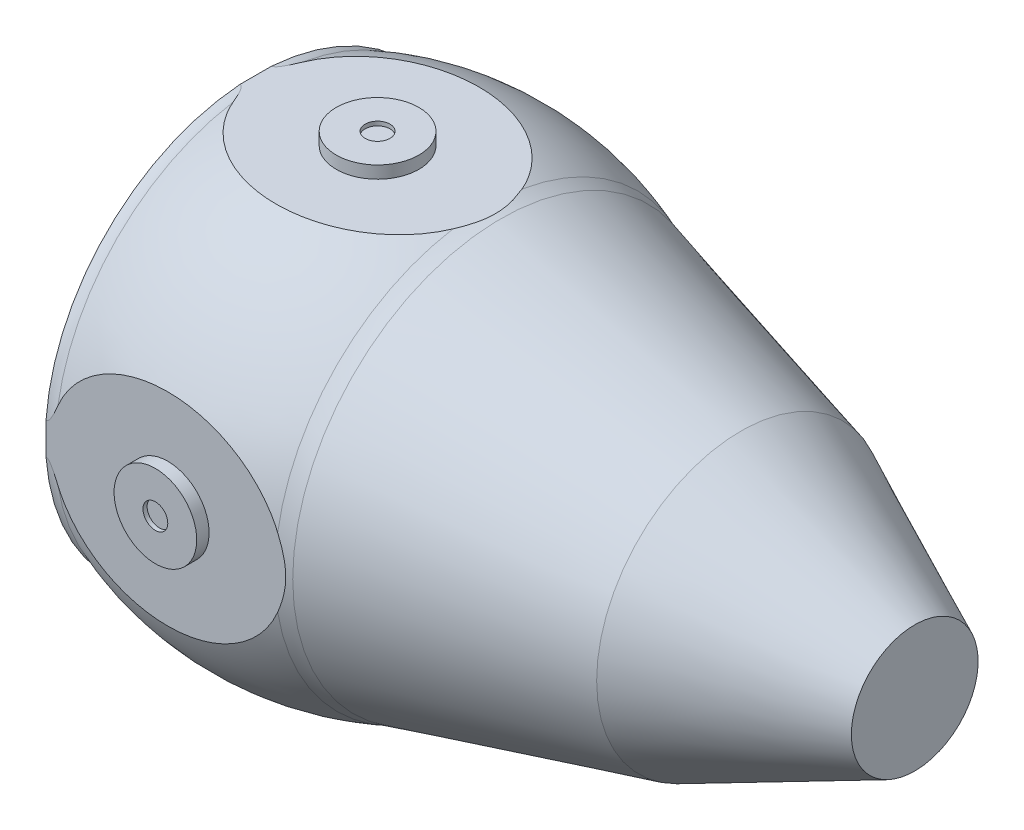
SolidWorks part; units mm, degrees
material "ABS"
ref_plane "Plano frontal" through (0, 0, 0) normal (0, 0, 1) x (1, 0, 0)
ref_plane "Plano superior" through (0, 0, 0) normal (0, 1, 0) x (1, 0, 0)
ref_plane "Plano direito" through (0, 0, 0) normal (1, 0, 0) x (0, 0, -1)
sketch "Esboço1" plane through (0, 0, 0) normal (0, 0, 1) x (1, 0, 0)
  line L0 (0, 0) -> (0, 2210.2124) construction
  line L1 (0, 0) -> (169.4374, 0) construction
  line L2 (3250.5369, 0) -> (3250.5369, 383.5)
  line L3 (3250.5369, 383.5) -> (2198.5369, 873)
  line L4 (2198.5369, 873) -> (746.5369, 1260)
  line L5 (0, -439.8614) -> (665, 1286.4859) construction
  line L6 (0, -439.8614) -> (-665, 1286.4859) construction
  line L7 (-736.8919, 1273.118) -> (-1420, 1273.118) construction
  line L8 (-3866.8673, 2245.4829) -> (-3866.8673, 0) construction
  line L9 (-169.4374, 0) -> (169.4374, 0) construction
  line L10 (-1420, 1273.118) -> (-3610, 2160) construction
  line L11 (-3866.8673, 2245.4829) -> (-3861.047, 2245.4829) construction
  line L12 (-3866.8673, 2378.8809) -> (-3991.8673, 2378.8809) construction
  line L13 (-1422.922, 1258.118) -> (-3618.297, 2147.1767) construction
  line L14 (-6965, 15) -> (3235.5369, 15) construction
  line L15 (2193.4021, 858.8449) -> (742.6738, 1245.506) construction
  line L16 (-6630, 350) -> (2492.8949, 350) construction
  line L17 (-736.8919, 1258.118) -> (-1422.922, 1258.118) construction
  line L18 (-4829, 2860) -> (-6980, 3864) construction
  line L19 (-4834.2705, 2845.9065) -> (-6965, 3840.4451) construction
  line L20 (-6980, 0) -> (3250.5369, 0) construction
  line L21 (-3991.8673, 0) -> (-3866.8673, 0) construction
  line L22 (3235.5369, 0) -> (-3866.8673, 0) construction
  line L23 (3235.5369, 373.9352) -> (2193.4021, 858.8449)
  line L24 (2193.4021, 858.8449) -> (1303.3383, 1096.0727)
  line L25 (-1317.1289, 1258.118) -> (-1422.922, 1258.118) construction
  line L26 (-1422.922, 1258.118) -> (-3861.047, 2245.4829) construction
  line L27 (-3991.8673, 2378.8809) -> (-3991.8673, 0) construction
  line L28 (-1317.1289, 1258.118) -> (-736.8919, 923.118) construction
  line L29 (656.3984, 921.8062) -> (746.5369, 946.0868) construction
  line L30 (3250.5369, 0) -> (3235.5369, 0)
  line L31 (-736.8919, 923.118) -> (-1488.1803, 923.118) construction
  line L32 (-1488.1803, 923.118) -> (-3805.5661, 1861.5873) construction
  line L33 (-4951.2113, 2530.7942) -> (-6630, 3314.385) construction
  line L34 (-6630, 3314.385) -> (-6630, 350) construction
  line L35 (2078.7249, 542.715) -> (656.3984, 921.8062) construction
  line L36 (2492.8949, 350) -> (2078.7249, 542.715) construction
  line L37 (2492.8949, 350) -> (2492.8949, 350) construction
  line L38 (-6965, 3840.4451) -> (-6965, 15) construction
  line L39 (-6980, 3864) -> (-6980, 0) construction
  line L40 (3235.5369, 0) -> (3235.5369, 373.9352)
  line L41 (746.5369, 1260) -> (746.5369, 1244.4764) construction
  line L42 (3235.5369, 15) -> (3235.5369, 373.9352) construction
  line L43 (746.5369, 946.0868) -> (1303.3383, 1096.0727) construction
  line L44 (1303.3383, 1096.0727) -> (746.5369, 1244.4764)
  line L45 (746.5369, 1244.4764) -> (746.5369, 946.0868) construction
  line L46 (746.5369, 1244.4764) -> (71.7181, 1244.4764)
  line L47 (-736.8919, 1273.118) -> (-736.8919, 1244.4764)
  line L48 (41.7181, 1244.4764) -> (41.7181, 1164.4764)
  line L49 (41.7181, 1164.4764) -> (71.7181, 1164.4764)
  line L50 (71.7181, 1164.4764) -> (71.7181, 1244.4764)
  line L51 (41.7181, 1244.4764) -> (-736.8919, 1244.4764)
  arc A0 (665, 1286.4859) -> (-665, 1286.4859) centre (0, -439.8614) ccw
  arc A1 (746.5369, 1260) -> (665, 1286.4859) centre (952.5676, 2033.0145) cw
  arc A2 (-736.8919, 1273.118) -> (-665, 1286.4859) centre (-736.8919, 1473.118) ccw
  arc A3 (-3610, 2160) -> (-3866.8673, 2378.8809) centre (-5637.2528, 41.0847) ccw construction
  arc A4 (656.3984, 921.8062) -> (539.1892, 959.8796) centre (952.5676, 2033.0145) cw construction
  arc A5 (539.1892, 959.8796) -> (-539.1892, 959.8796) centre (0, -439.8614) ccw construction
  arc A6 (-736.8919, 923.118) -> (-539.1892, 959.8796) centre (-736.8919, 1473.118) ccw construction
  arc A8 (659.6081, 1272.4885) -> (-659.6081, 1272.4885) centre (0, -439.8614) ccw construction
  arc A9 (-3618.297, 2147.1767) -> (-4834.2705, 2845.9065) centre (-5637.2528, 41.0847) ccw construction
  arc A10 (-3610, 2160) -> (-4829, 2860) centre (-5637.2528, 41.0847) ccw construction
  arc A12 (-3805.5661, 1861.5873) -> (-4951.2113, 2530.7942) centre (-5637.2528, 41.0847) ccw construction
  arc A13 (742.6738, 1245.506) -> (659.6081, 1272.4885) centre (952.5676, 2033.0145) cw construction
  arc A14 (-736.8919, 1258.118) -> (-659.6081, 1272.4885) centre (-736.8919, 1473.118) ccw construction
  point P17 (-4829, 2860)
  point P56 (-8569.7525, 41.0847)
  dimension "D1" = 800
  dimension "D7" = 1850
  dimension "D9" = 200
  dimension "D11" = 3610
  dimension "D14" = 2160
  dimension "D15" = 5865
  dimension "D2" = 767
  dimension "D3" = 1746
  dimension "D4" = 1052
  dimension "D5" = 2520
  dimension "D6" = 1452
  dimension "D8" = 1330
  dimension "D10" = 1420
  dimension "D12" = 4829
  dimension "D13" = 2860
  dimension "D16" = 5.8203
  dimension "D17" = 125
  dimension "D20" = 150
  dimension "D21" = 150
  dimension "D22" = 7242.4042
  dimension "D23" = 125
  dimension "D24" = 808.61
  dimension "D25" = 30
  dimension "D26" = 80
  dimension "D18" = 350
  dimension "D19" = 15
revolve "Revolução1" add sketch "Esboço1" angle 360 about L9
scale "Escala1" scale about origin uniform scaling yes scale factor 0.2
sketch "Esboço2" plane through (0, 0, 0) normal (0, 0, 1) x (1, 0, 0)
  line L0 (149.3074, 248.8953) -> (14.3436, 248.8953) construction
  line L2 (15, 268.8953) -> (15, 263.8953)
  line L3 (15, 263.8953) -> (0, 263.8953)
  line L4 (15, 268.8953) -> (50, 268.8953)
  line L5 (50, 268.8953) -> (50, 253.8953)
  line L6 (50, 253.8953) -> (175.533, 253.8953)
  line L8 (175.533, 253.8953) -> (175.533, 311.1464)
  line L11 (0, 311.1464) -> (175.533, 311.1464)
  line L12 (0, -141.1401) -> (0, 141.1401) construction
  line L13 (0, 263.8953) -> (0, 311.1464)
  point P20 (0, 0)
  dimension "D1" = 15
  dimension "D2" = 5
  dimension "D3" = 100
  dimension "D4" = 30
  dimension "D5" = 5
revolve "Corte-Revolução9" cut sketch "Esboço2" angle 360 about L12
hole_wizard "Rebaixo para parafuso Allen sextavado de M61" positions "Esboço8" profile "Esboço7" counterbore size "M6" standard "DIN"
sketch "Esboço8" plane through (0, 263.8953, 0) normal (0, 1, 0) x (1, 0, 0)
  point P0 (0, 0)
sketch "Esboço7" plane through (0, 263.8953, 0) normal (1, 0, 0) x (0, 0, 1)
  line L0 (0, 0) -> (0, 16.9828)
  line L1 (0, 16.9828) -> (3.3, 15)
  line L2 (3.3, 15) -> (3.3, 6.4)
  line L3 (3.3, 6.4) -> (5.5, 6.4)
  line L4 (5.5, 6.4) -> (5.5, 0)
  line L5 (5.5, 0) -> (0, 0)
  line L10 (0, 16.9828) -> (-3.3, 15) construction
  line L11 (0, -6.35) -> (0, 107.95) construction
  dimension "Hole Dia." = 6.6
  dimension "Hole Depth" = 15
  dimension "C'Bore Dia." = 11
  dimension "C'Bore Depth" = 6.4
  dimension "Drill Angle" = 118
pattern_circular "PadrãoCircular1" count 4 over 360 about axis through (0, 0, 0) along (1, 0, 0) of "Corte-Revolução9", "Rebaixo para parafuso Allen sextavado de M61"
hole_wizard "Furo com folga de M61" positions "Esboço9" profile "Esboço10" hole size "M6" standard "Ansi Metric"
sketch "Esboço9" plane through (14.3436, 0, 0) normal (1, 0, 0) x (0, 0, -1)
  line L0 (0, 248.8953) -> (0, 232.8953) construction
  point P9 (0, 240.8953)
  point P14 (240.8953, 0)
  point P15 (0, -240.8953)
  point P16 (-240.8953, 0)
  point P17 (0, 0)
sketch "Esboço10" plane through (14.3436, 240.8953, 0) normal (0, 1, 0) x (0, 0, -1)
  line L0 (0, 0) -> (0, 21.3255)
  line L1 (0, 21.3255) -> (3.3, 19.3426)
  line L2 (3.3, 19.3426) -> (3.3, 0)
  line L3 (3.3, 0) -> (0, 0)
  line L4 (0, 21.3255) -> (-3.3, 19.3426) construction
  line L5 (0, -6.35) -> (0, 107.95) construction
  dimension "Hole Dia." = 6.6
  dimension "Hole Depth" = 19.3426
  dimension "Drill Angle" = 118
